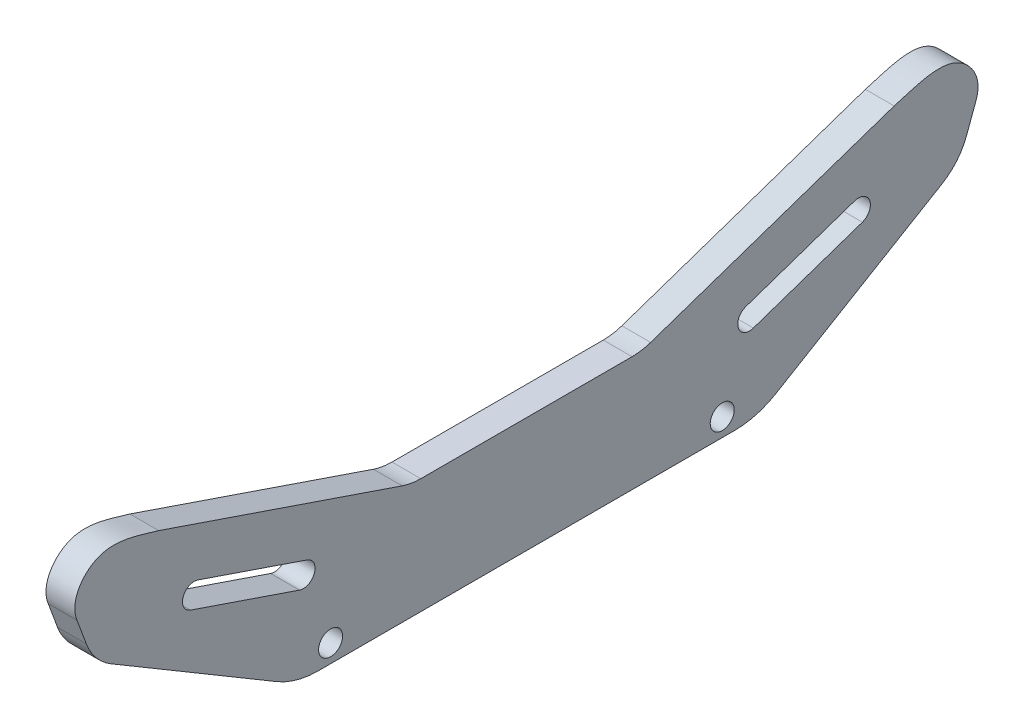
SolidWorks part; units mm, degrees
material "Pine"
ref_plane "Front Plane" through (0, 0, 0) normal (0, 0, 1) x (1, 0, 0)
ref_plane "Top Plane" through (0, 0, 0) normal (0, 1, 0) x (1, 0, 0)
ref_plane "Right Plane" through (0, 0, 0) normal (1, 0, 0) x (0, 0, -1)
sketch "Sketch1" plane through (0, 0, 0) normal (1, 0, 0) x (0, 0, -1)
  line L0 (50.8, 0) -> (-50.8, 0)
  line L1 (-50.8, 0) -> (-95.4919, 26.5106)
  line L2 (-95.4919, 26.5106) -> (-99.0952, 36.2672)
  line L3 (-81.0957, 44.3839) -> (-25.4, 25.4)
  line L4 (-25.4, 25.4) -> (25.4, 25.4)
  line L5 (0, 0) -> (0, 25.4) construction
  line L6 (50.8, 0) -> (95.4919, 26.5106)
  line L7 (81.0957, 44.3839) -> (25.4, 25.4)
  line L8 (95.4919, 26.5106) -> (99.0952, 36.2672)
  circle A0 centre (0, 109.8878) radius 101.6 construction
  circle A1 centre (0, 138.5431) radius 127 construction
  spline S0 degree 3 poles (-81.0957, 44.3839) (-84.7934, 45.3677) (-94.5547, 49.4797) (-100.7878, 40.4842) (-99.0952, 36.2672) knots 0 0 0 0 0.528782 1 1 1 1
  spline S1 degree 3 poles (81.0957, 44.3839) (84.7934, 45.3677) (94.5547, 49.4797) (100.7878, 40.4842) (99.0952, 36.2672) knots 0 0 0 0 0.528782 1 1 1 1
  dimension "D1" = 203.2
  dimension "D5" = 254
  dimension "D2" = 50.8
  dimension "D3" = 25.4
  dimension "D4" = 25.4
extrude "Boss-Extrude1" add sketch "Sketch1" along normal blind 6.35
sketch "Sketch2" plane through (0, 0, 0) normal (-1, 0, 0) x (0, 0, 1)
  line L0 (-73.2438, 28.1541) -> (-49.202, 19.9595) construction
  line L1 (-72.405, 30.6151) -> (-48.3632, 22.4205)
  line L2 (-74.0826, 25.6932) -> (-50.0408, 17.4985)
  line L3 (-81.0957, 44.3839) -> (-25.4, 25.4) construction
  line L4 (0, 0) -> (0, 25.4) construction
  line L5 (73.2438, 28.1541) -> (49.202, 19.9595) construction
  line L6 (72.405, 30.6151) -> (48.3632, 22.4205)
  line L7 (74.0826, 25.6932) -> (50.0408, 17.4985)
  arc A0 (-72.405, 30.6151) -> (-74.0826, 25.6932) centre (-73.2438, 28.1541) ccw
  arc A1 (-50.0408, 17.4985) -> (-48.3632, 22.4205) centre (-49.202, 19.9595) ccw
  arc A2 (72.405, 30.6151) -> (74.0826, 25.6932) centre (73.2438, 28.1541) cw
  arc A3 (50.0408, 17.4985) -> (48.3632, 22.4205) centre (49.202, 19.9595) cw
  point P2 (-61.2229, 24.0568)
  point P15 (61.2229, 24.0568)
  dimension "D2" = 2.6
  dimension "D1" = 25.4
extrude "slots" cut sketch "Sketch2" against normal through all
sketch "Sketch3" plane through (0, 0, 0) normal (-1, 0, 0) x (0, 0, 1)
  line L0 (50.8, 0) -> (-50.8, 0) construction
  circle A0 centre (-43.18, 4) radius 2.65
  circle A1 centre (43.18, 4) radius 2.65
  dimension "D2" = 5.3
  dimension "D1" = 4
  dimension "D3" = 43.18
  dimension "D4" = 43.18
extrude "holes" cut sketch "Sketch3" against normal through all
fillet "Fillet1" radius 12.7 4 edges at (3.175, 25.4, -25.4) (3.175, 25.4, 25.4) (3.175, 26.5106, 95.4919) (3.175, 26.5106, -95.4919)
fillet "Fillet2" radius 17.78 2 edges at (3.175, 0, 50.8) (3.175, 0, -50.8)
sketch "bearing" plane through (0, 0, 0) normal (-1, 0, 0) x (0, 0, 1)
  line L0 (0, 0) -> (0, 0.8413) construction
  circle A0 centre (-65.2443, 25.3841) radius 7.9375 construction
  circle A1 centre (65.2443, 25.3841) radius 7.9375 construction
  dimension "D1" = 15.875
sketch "spools" plane through (0, 0, 0) normal (-1, 0, 0) x (0, 0, 1)
  circle A0 centre (0, 113.8416) radius 101.6 construction
  circle A1 centre (0, 144.5742) radius 127 construction
  dimension "D1" = 203.2
  dimension "D2" = 254
